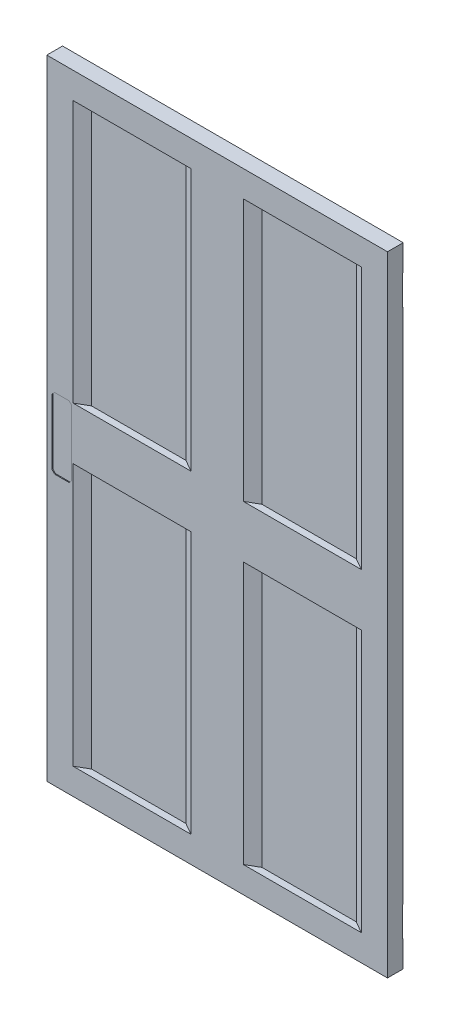
SolidWorks part; units mm, degrees
ref_plane "Front Plane" through (0, 0, 0) normal (0, 0, 1) x (1, 0, 0)
ref_plane "Top Plane" through (0, 0, 0) normal (0, 1, 0) x (1, 0, 0)
ref_plane "Right Plane" through (0, 0, 0) normal (1, 0, 0) x (0, 0, -1)
sketch "Sketch1" plane through (0, 0, 0) normal (0, 0, 1) x (1, 0, 0)
  line L1 (-559.6685, 1413.8122) -> (740.3315, 1413.8122)
  line L2 (-559.6685, 1413.8122) -> (-559.6685, -986.1878)
  line L3 (-559.6685, -986.1878) -> (740.3315, -986.1878)
  line L4 (740.3315, 1413.8122) -> (740.3315, -986.1878)
  dimension "D1" = 2400
  dimension "D2" = 1300
extrude "Boss-Extrude1" add sketch "Sketch1" along normal blind 60
sketch "Sketch4" plane through (740.3315, 0, 0) normal (1, 0, 0) x (0, 0, -1)
  line L0 (0, 213.8122) -> (-60, 213.8122) construction
  line L1 (0, -986.1878) -> (0, 1413.8122) construction
  line L2 (-60, -986.1878) -> (-60, 1413.8122) construction
ref_plane "Plane1" through (0, 213.8122, 0) normal (0, -1, 0) x (-1, 0, 0)
sketch "Sketch5" plane through (0, 213.8122, 0) normal (0, -1, 0) x (-1, 0, 0)
  line L1 (-190.3315, 0) -> (-235.3648, -26)
  line L2 (-595.2982, -26) -> (-235.3648, -26)
  line L7 (559.6685, 0) -> (-740.3315, 0) construction
  line L12 (-640.3315, 0) -> (-595.2982, -26)
  line L19 (9.6685, 0) -> (459.6685, 0)
  line L20 (-640.3315, 0) -> (-190.3315, 0)
  line L22 (9.6685, 0) -> (54.7018, -26)
  line L23 (54.7018, -26) -> (414.6352, -26)
  line L24 (414.6352, -26) -> (459.6685, 0)
  line L25 (-740.3315, -30) -> (559.6685, -30) construction
  line L26 (-740.3315, 0) -> (-740.3315, -60) construction
  line L27 (559.6685, -60) -> (559.6685, 0) construction
  line L28 (559.6685, -60) -> (-740.3315, -60) construction
  line L29 (414.6352, -34) -> (459.6685, -60)
  line L30 (54.7018, -34) -> (414.6352, -34)
  line L31 (9.6685, -60) -> (459.6685, -60)
  line L32 (9.6685, -60) -> (54.7018, -34)
  line L33 (-190.3315, -60) -> (-235.3648, -34)
  line L34 (-640.3315, -60) -> (-595.2982, -34)
  line L35 (-640.3315, -60) -> (-190.3315, -60)
  line L36 (-595.2982, -34) -> (-235.3648, -34)
  point P0 (-90.3315, 0)
  dimension "D1" = 100
  dimension "D2" = 100
  dimension "D3" = 150
  dimension "D4" = 150
  dimension "D5" = 100
  dimension "D6" = 150
  dimension "D7" = 150
  dimension "D8" = 34
  dimension "D9" = 30
  dimension "D10" = 100
  dimension "D11" = 34
extrude "Cut-Extrude4" cut sketch "Sketch5" against normal blind 1100 and the other way blind 1100
sketch "Sketch6" plane through (0, 213.8122, 0) normal (0, -1, 0) x (-1, 0, 0)
  line L0 (-190.3315, 0) -> (-235.3648, -26)
  line L1 (-595.2982, -26) -> (-235.3648, -26)
  line L2 (-640.3315, 0) -> (-595.2982, -26)
  line L3 (9.6685, 0) -> (459.6685, 0)
  line L4 (-640.3315, 0) -> (-190.3315, 0)
  line L5 (9.6685, 0) -> (54.7018, -26)
  line L6 (54.7018, -26) -> (414.6352, -26)
  line L7 (414.6352, -26) -> (459.6685, 0)
  line L8 (-740.3315, -30) -> (559.6685, -30) construction
  line L9 (414.6352, -34) -> (459.6685, -60)
  line L10 (-740.3315, 0) -> (-740.3315, -60) construction
  line L11 (559.6685, -60) -> (559.6685, 0) construction
  line L12 (54.7018, -34) -> (414.6352, -34)
  line L13 (559.6685, 0) -> (-740.3315, 0) construction
  line L14 (559.6685, -60) -> (-740.3315, -60) construction
  line L15 (9.6685, -60) -> (459.6685, -60)
  line L16 (9.6685, -60) -> (54.7018, -34)
  line L17 (-190.3315, -60) -> (-235.3648, -34)
  line L18 (-640.3315, -60) -> (-190.3315, -60)
  line L19 (-640.3315, -60) -> (-595.2982, -34)
  line L20 (-595.2982, -34) -> (-235.3648, -34)
  point P18 (-90.3315, 0)
  dimension "D1" = 150
  dimension "D2" = 150
  dimension "D3" = 150
  dimension "D4" = 150
  dimension "D5" = 100
  dimension "D6" = 100
  dimension "D7" = 100
  dimension "D8" = 100
  dimension "D9" = 34
  dimension "D10" = 34
  dimension "D11" = 30
  dimension "D12" = 30
extrude "Boss-Extrude2" add sketch "Sketch6" along normal blind 100 and the other way blind 100
sketch "Sketch7" plane through (0, 0, 0) normal (0, 0, -1) x (-1, 0, 0)
  line L0 (-740.3315, -986.1878) -> (-740.3315, 1413.8122) construction
  line L1 (-740.3315, 1313.8122) -> (-684.8315, 1313.8122)
  line L2 (-740.3315, 1313.8122) -> (-740.3315, 1199.8122)
  line L3 (-740.3315, 1199.8122) -> (-684.8315, 1199.8122)
  line L4 (-684.8315, 1313.8122) -> (-684.8315, 1199.8122)
  line L5 (-740.3315, 1413.8122) -> (559.6685, 1413.8122) construction
  line L6 (-740.3315, -772.1878) -> (-740.3315, -886.1878)
  line L7 (-740.3315, -772.1878) -> (-684.8315, -772.1878)
  line L8 (-684.8315, -772.1878) -> (-684.8315, -886.1878)
  line L9 (-740.3315, -886.1878) -> (-684.8315, -886.1878)
  line L10 (559.6685, 1413.8122) -> (559.6685, -986.1878) construction
  line L11 (474.6685, 313.8122) -> (529.6685, 313.8122)
  line L12 (464.6685, 303.8122) -> (464.6685, 53.8122)
  line L13 (474.6685, 43.8122) -> (529.6685, 43.8122)
  line L14 (539.6685, 303.8122) -> (539.6685, 53.8122)
  line L16 (464.6685, 303.8122) -> (474.6685, 313.8122)
  line L17 (529.6685, 313.8122) -> (539.6685, 303.8122)
  line L18 (464.6685, 53.8122) -> (474.6685, 43.8122)
  line L19 (529.6685, 43.8122) -> (539.6685, 53.8122)
  point P8 (464.6685, 313.8122)
  point P10 (539.6685, 43.8122)
  point P14 (464.6685, 43.8122)
  point P15 (539.6685, 313.8122)
  dimension "D1" = 100
  dimension "D2" = 55.5
  dimension "D3" = 114
  dimension "D5" = 20
  dimension "D6" = 60
  dimension "D7" = 270
  dimension "D12" = 100
  dimension "D13" = 75
  dimension "D4" = 2
extrude "Cut-Extrude5" cut sketch "Sketch7" against normal blind 3.4
sketch "Sketch10" plane through (0, 0, 60) normal (0, 0, 1) x (1, 0, 0)
  line L0 (-529.6685, 313.8122) -> (-474.6685, 313.8122)
  line L1 (-539.6685, 303.8122) -> (-539.6685, 53.8122)
  line L2 (-529.6685, 43.8122) -> (-474.6685, 43.8122)
  line L3 (-464.6685, 303.8122) -> (-464.6685, 53.8122)
  line L4 (-539.6685, 303.8122) -> (-529.6685, 313.8122)
  line L5 (-474.6685, 313.8122) -> (-464.6685, 303.8122)
  line L6 (-539.6685, 53.8122) -> (-529.6685, 43.8122)
  line L7 (-474.6685, 43.8122) -> (-464.6685, 53.8122)
  line L8 (-559.6685, 1413.8122) -> (-559.6685, -986.1878) construction
  point P0 (-539.6685, 313.8122)
  point P1 (-464.6685, 43.8122)
  point P2 (-539.6685, 43.8122)
  point P3 (-464.6685, 313.8122)
  dimension "D1" = 10
  dimension "D2" = 10
  dimension "D3" = 10
  dimension "D4" = 10
  dimension "D5" = 10
  dimension "D6" = 10
  dimension "D7" = 10
  dimension "D8" = 10
  dimension "D9" = 270
  dimension "D10" = 75
  dimension "D11" = 20
  dimension "D12" = 60
extrude "Cut-Extrude6" cut sketch "Sketch10" against normal blind 3.4
sketch "Sketch13" plane through (0, 0, 0) normal (0, 0, -1) x (-1, 0, 0)
  line L1 (-596.6868, -932.8461) -> (-401.6868, -932.8461)
  line L2 (-596.6868, -932.8461) -> (-596.6868, -972.8461)
  line L3 (-596.6868, -972.8461) -> (-401.6868, -972.8461)
  line L4 (-401.6868, -932.8461) -> (-401.6868, -972.8461)
  dimension "D1" = 195
  dimension "D2" = 40
extrude "Cut-Extrude7" cut sketch "Sketch13" against normal blind 5
